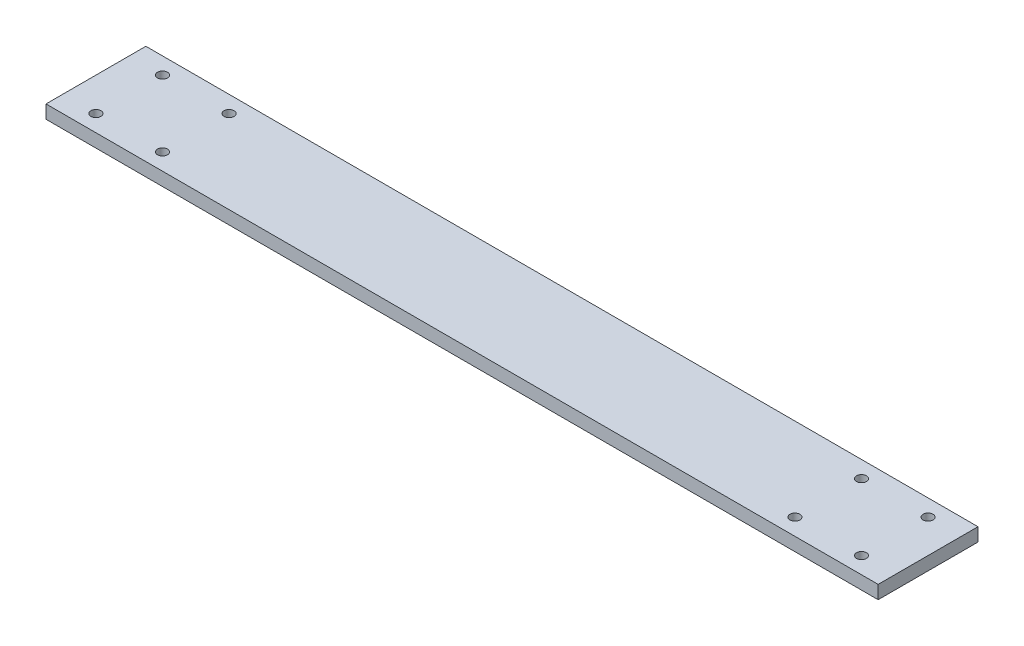
SolidWorks part; units mm, degrees
ref_plane "Ebene vorne" through (0, 0, 0) normal (0, 0, 1) x (1, 0, 0)
ref_plane "Ebene oben" through (0, 0, 0) normal (0, 1, 0) x (1, 0, 0)
ref_plane "Ebene rechts" through (0, 0, 0) normal (1, 0, 0) x (0, 0, -1)
sketch "Skizze1" plane through (0, 0, 0) normal (0, 1, 0) x (1, 0, 0)
  line L0 (0, 15) -> (0, -15) construction
  line L1 (125, -15) -> (-125, -15)
  line L2 (125, -15) -> (125, 15)
  line L3 (125, 15) -> (-125, 15)
  line L4 (-125, -15) -> (-125, 15)
  line L5 (125, -15) -> (-125, 15) construction
  line L6 (125, 15) -> (-125, -15) construction
  circle A0 centre (-115, 10) radius 1.5
  circle A1 centre (-115, -10) radius 1.5
  circle A2 centre (-95, -10) radius 1.5
  circle A3 centre (-95, 10) radius 1.5
  circle A4 centre (95, -10) radius 1.5
  circle A5 centre (115, -10) radius 1.5
  circle A6 centre (115, 10) radius 1.5
  circle A7 centre (95, 10) radius 1.5
  point P0 (0, 0)
  dimension "D2" = 3
  dimension "D3" = 3
  dimension "D4" = 3
  dimension "D5" = 3
  dimension "D1" = 30
  dimension "D6" = 20
  dimension "D7" = 20
  dimension "D8" = 20
  dimension "D9" = 20
  dimension "D10" = 10
  dimension "D11" = 5
  dimension "D12" = 5
  dimension "D13" = 10
  dimension "D14" = 190
extrude "Aufsatz-Linear austragen1" add sketch "Skizze1" along normal blind 4
